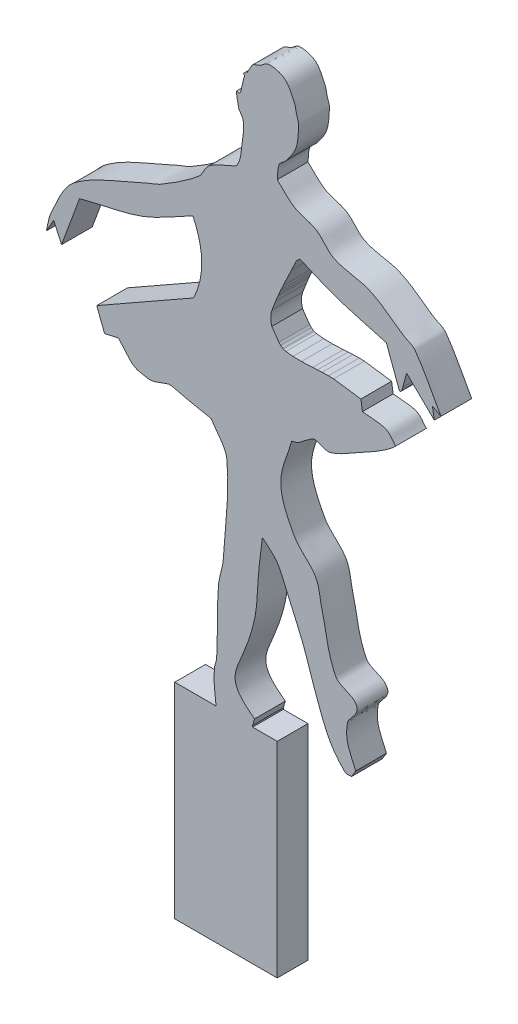
SolidWorks part; units mm, degrees
ref_plane "Alzado" through (0, 0, 0) normal (0, 0, 1) x (1, 0, 0)
ref_plane "Planta" through (0, 0, 0) normal (0, 1, 0) x (1, 0, 0)
ref_plane "Vista lateral" through (0, 0, 0) normal (1, 0, 0) x (0, 0, -1)
sketch "Croquis4" plane through (0, 0, 0) normal (0, 0, 1) x (1, 0, 0)
  line L0 (1069.8862, -9982.1073) -> (1096.5761, -9982.1073) construction
  line L1 (1102.5614, -9982.0997) -> (1101.7304, -9981.6452)
  line L3 (1101.7304, -9981.6452) -> (1101.914, -9982.7471)
  line L4 (1101.914, -9982.7471) -> (1099.2069, -9980.1163)
  line L5 (1099.2069, -9980.1163) -> (1098.8413, -9981.4945)
  line L7 (1098.4831, -9981.9057) -> (1097.2342, -9978.547)
  line L8 (1094.7459, -9984.5391) -> (1094.8984, -9985.5305)
  line L9 (1094.2502, -10016.2238) -> (1093.8308, -10016.9101)
  line L10 (1084.375, -10016.7576) -> (1084.1843, -10017.4058)
  line L12 (1071.1055, -9991.2124) -> (1069.7328, -9991.5175)
  line L13 (1069.7328, -9991.5175) -> (1068.9703, -9989.5348)
  line L14 (1068.9703, -9989.5348) -> (1078.4261, -9984.1587)
  line L15 (1067.2926, -9981.3372) -> (1065.5387, -9986.1032)
  line L16 (1065.5387, -9986.1032) -> (1064.7761, -9984.4256)
  line L17 (1064.7761, -9984.4256) -> (1064.0517, -9985.6838)
  line L19 (1083.4028, -9962.9472) -> (1083.3065, -9962.7305)
  line L20 (1083.3065, -9962.7305) -> (1083.5734, -9962.4636)
  line L21 (1083.5734, -9962.4636) -> (1083.6497, -9962.5018)
  line L27 (1084.1843, -10017.4058) -> (1084.375, -10016.7576)
  line L28 (1057.3314, -9960.8458) -> (1057.3314, -10026.2108)
  line L29 (1080.5994, -10017.3685) -> (1080.6272, -10017.5493)
  line L30 (1076.5856, -10017.5493) -> (1080.6272, -10017.5493)
  line L35 (1076.5856, -10017.5493) -> (1076.5856, -10037.5493)
  line L36 (1076.5856, -10037.5493) -> (1086.5856, -10037.5493)
  line L37 (1086.5856, -10017.5493) -> (1086.5856, -10037.5493)
  line L38 (1084.1843, -10017.4058) -> (1084.1843, -10017.5493)
  line L39 (1084.1843, -10017.5493) -> (1086.5856, -10017.5493)
  line L40 (1094.7459, -9984.5391) -> (1092.0915, -9984.1685)
  line L41 (1092.0915, -9984.1685) -> (1091.5875, -9984.1566)
  line L42 (1091.5875, -9984.1566) -> (1090.9595, -9984.173)
  line L43 (1090.9595, -9984.173) -> (1090.5104, -9984.1966)
  line L44 (1090.5104, -9984.1966) -> (1090.0409, -9984.2251)
  line L45 (1090.0409, -9984.2251) -> (1088.9419, -9984.2732)
  line L46 (1088.9419, -9984.2732) -> (1088.1172, -9984.2538)
  line L47 (1088.1172, -9984.2538) -> (1087.4347, -9984.1733)
  line L48 (1087.4347, -9984.1733) -> (1087.1951, -9984.1113)
  line L49 (1087.1951, -9984.1113) -> (1087.1127, -9984.071)
  line L50 (1087.1127, -9984.071) -> (1086.9204, -9983.9308)
  line L51 (1086.9204, -9983.9308) -> (1086.7524, -9983.7528)
  line L52 (1086.7524, -9983.7528) -> (1086.0567, -9982.7471)
  line L53 (1086.0805, -9981.3372) -> (1086.431, -9980.4183)
  line L54 (1086.431, -9980.4183) -> (1086.6588, -9979.8715)
  line L55 (1086.6588, -9979.8715) -> (1086.785, -9979.5803)
  line L56 (1086.785, -9979.5803) -> (1086.946, -9979.2181)
  line L57 (1086.946, -9979.2181) -> (1087.1661, -9978.7366)
  line L58 (1087.1661, -9978.7366) -> (1087.9738, -9977.0327)
  line L59 (1087.9738, -9977.0327) -> (1088.4623, -9975.9968)
  line L61 (1092.8353, -9977.2977) -> (1094.6199, -9977.8259)
  line L62 (1094.6199, -9977.8259) -> (1095.769, -9978.1393)
  line L63 (1095.769, -9978.1393) -> (1097.2342, -9978.547)
  line L64 (1088.4623, -9975.9968) -> (1088.8004, -9975.6775)
  spline S0 degree 3 poles (1083.6497, -9962.5018) (1083.7591, -9962.2555) (1083.9978, -9961.7956) (1084.1835, -9961.5867) (1084.2975, -9961.4584) (1084.7754, -9961.341) (1084.9461, -9961.2435) (1085.228, -9961.0824) (1085.4602, -9960.7531) (1085.7849, -9960.7478) (1086.3156, -9960.7393) (1086.8987, -9960.87) (1087.31, -9961.2054) (1087.783, -9961.5911) (1087.9974, -9962.2193) (1088.2632, -9962.7687) (1088.3827, -9963.0156) (1088.3887, -9963.3028) (1088.4539, -9963.5693) (1088.5285, -9963.8748) (1088.6976, -9964.1704) (1088.6826, -9964.4844) (1088.5936, -9966.3536) (1088.4856, -9966.726) (1087.4625, -9968.0304) (1087.2629, -9968.2849) (1086.903, -9968.419) (1086.7762, -9968.7167) (1086.5952, -9969.1417) (1086.6491, -9969.6318) (1086.5856, -9970.0893) knots 0 0 0 0 1 1 1 2 2 2 3 3 3 4 4 4 5 5 5 6 6 6 7 7 7 8 8 8 9 9 9 10 10 10 10
  spline S1 degree 3 poles (1086.5856, -9970.0893) (1087.1448, -9970.585) (1087.627, -9971.1843) (1088.2632, -9971.5763) (1088.9042, -9971.9712) (1089.7198, -9972.0195) (1090.3603, -9972.4151) (1091.0347, -9972.8317) (1091.4383, -9973.6342) (1092.1523, -9973.9784) (1093.2469, -9974.506) (1094.5565, -9974.4613) (1095.6601, -9974.9697) (1096.8448, -9975.5155) (1097.8423, -9976.3991) (1098.9392, -9977.1049) (1099.304, -9977.3397) (1099.7902, -9977.4401) (1100.0449, -9977.7912) (1101.0213, -9979.1377) (1101.7226, -9980.6636) (1102.5614, -9982.0997) knots 0 0 0 0 1 1 1 2 2 2 3 3 3 4 4 4 5 5 5 6 6 6 7 7 7 7
  spline S2 degree 3 poles (1097.2342, -9978.547) (1095.5693, -9978.0641) (1093.8765, -9977.6684) (1092.2394, -9977.0981) (1091.0681, -9976.6901) (1089.9383, -9976.1731) (1088.8004, -9975.6775) knots 0 0 0 0 1 1 1 1.797437 1.797437 1.797437 1.797437
  spline S3 degree 3 poles (1098.4831, -9981.9057) (1098.5937, -9982.0964) (1098.7131, -9981.9593) (1098.8413, -9981.4945) knots 0.232918 0.232918 0.232918 0.232918 1 1 1 1
  spline S4 degree 3 poles (1094.8984, -9985.5305) (1095.661, -9985.6449) (1096.4702, -9985.5873) (1097.1861, -9985.8736) (1097.6033, -9986.0405) (1097.8216, -9986.5091) (1098.1393, -9986.8269) knots 0 0 0 0 1 1 1 2 2 2 2
  spline S5 degree 3 poles (1098.1393, -9986.8269) (1097.4278, -9987.5977) (1095.4058, -9988.7216) (1094.4409, -9989.2289) (1093.5403, -9989.7024) (1092.6853, -9990.327) (1091.6956, -9990.5634) (1091.1327, -9990.6979) (1090.4615, -9989.9755) (1089.9799, -9990.2965) (1088.1959, -9991.4858) (1089.1582, -9991.1468) (1087.9972, -9991.4785) knots 0 0 0 0 1 1 1 2 2 2 3 3 3 4 4 4 4
  spline S6 degree 3 poles (1087.9972, -9991.4785) (1087.6413, -9992.8511) (1086.8883, -9994.179) (1086.9296, -9995.5964) (1086.968, -9996.9142) (1087.5912, -9998.1775) (1088.226, -9999.333) (1088.7424, -10000.2729) (1089.7965, -10000.8388) (1090.323, -10001.7732) (1090.7225, -10002.4822) (1090.7262, -10003.3501) (1090.9331, -10004.1371) (1091.3743, -10005.8157) (1091.4763, -10007.6253) (1092.2676, -10009.1701) (1092.6066, -10009.8321) (1093.6246, -10009.85) (1094.1359, -10010.3902) (1094.9321, -10011.2315) (1093.5656, -10011.9451) (1093.4495, -10012.5254) (1093.1321, -10014.1127) (1093.6779, -10014.9109) (1094.2502, -10016.2238) knots 0 0 0 0 1 1 1 2 2 2 3 3 3 4 4 4 5 5 5 6 6 6 7 7 7 8 8 8 8
  spline S7 degree 3 poles (1093.8308, -10016.9101) (1093.6148, -10016.8847) (1093.3378, -10016.9864) (1093.1826, -10016.8339) (1091.7267, -10015.4026) (1091.2933, -10014.1866) (1090.5899, -10012.3347) (1089.889, -10010.4893) (1089.3884, -10008.564) (1088.5691, -10006.768) (1086.4028, -10002.0187) (1087.0812, -10002.6934) (1085.1376, -10001.0487) knots 0 0 0 0 1 1 1 2 2 2 3 3 3 4 4 4 4
  spline S8 degree 3 poles (1085.1376, -10001.0487) (1085.0232, -10001.9892) (1084.8931, -10002.928) (1084.7944, -10003.8702) (1084.6389, -10005.3557) (1084.6934, -10006.872) (1084.375, -10008.3313) (1083.2252, -10013.6011) (1080.7341, -10014.0607) (1084.375, -10016.7576) knots 0 0 0 0 1 1 1 2 2 2 3 3 3 3
  spline S9 degree 3 poles (1080.5994, -10017.3685) (1080.4585, -10016.3352) (1080.3425, -10015.2751) (1080.485, -10014.242) (1080.5208, -10013.9824) (1080.6625, -10013.7411) (1080.6757, -10013.4794) (1080.7772, -10011.4605) (1080.7123, -10009.4351) (1080.8282, -10007.417) (1080.8801, -10006.5136) (1081.2722, -10005.6514) (1081.3239, -10004.748) (1081.4871, -10001.8907) (1081.9661, -9999.0154) (1081.667, -9996.1691) (1081.5599, -9995.1501) (1080.6503, -9994.3898) (1080.1419, -9993.5001) knots 0 0 0 0 1 1 1 2 2 2 3 3 3 4 4 4 5 5 5 6 6 6 6
  spline S10 degree 3 poles (1080.1419, -9993.5001) (1079.1918, -9993.3325) (1078.2617, -9993.1328) (1077.3204, -9992.9282) (1076.8893, -9992.8345) (1076.4649, -9992.6447) (1076.024, -9992.6613) (1075.7269, -9992.6725) (1074.6048, -9993.3114) (1073.9651, -9993.1951) (1073.4979, -9993.1102) (1072.9827, -9993.0844) (1072.5925, -9992.8138) (1071.9938, -9992.3988) (1071.6011, -9991.7462) (1071.1055, -9991.2124) knots 0 0 0 0 1 1 1 2 2 2 3 3 3 4 4 4 5 5 5 5
  spline S11 degree 2 poles (1078.4261, -9984.1587) (1080.0512, -9980.7931) (1078.3499, -9977.2574) knots 0 0 0 0.498057 0.498057 0.498057
  spline S12 degree 3 poles (1078.3499, -9977.2574) (1076.7358, -9978.0836) (1075.2008, -9979.0872) (1073.5075, -9979.7358) (1071.5098, -9980.5011) (1069.3496, -9980.7495) (1067.2926, -9981.3372) knots 0 0 0 0 1 1 1 2 2 2 2
  spline S13 degree 3 poles (1064.0517, -9985.6838) (1064.2207, -9985.0586) (1064.2692, -9984.3874) (1064.5587, -9983.8081) (1065.1797, -9982.5655) (1065.6593, -9981.1184) (1066.7579, -9980.2685) (1068.7451, -9978.731) (1071.238, -9977.992) (1073.4972, -9976.8927) (1074.0915, -9976.6035) (1074.7495, -9976.444) (1075.3163, -9976.1041) (1076.5587, -9975.3589) (1077.7919, -9974.5793) (1078.9037, -9973.6504) (1079.3427, -9973.2837) (1079.4744, -9972.6297) (1079.9135, -9972.2632) (1080.4284, -9971.8334) (1081.1034, -9971.6438) (1081.6923, -9971.3226) (1082.0369, -9971.1346) (1082.5236, -9971.0796) (1082.7134, -9970.736) (1083.0608, -9970.1073) (1083.08, -9969.3435) (1083.1791, -9968.6321) (1083.2651, -9968.0141) (1083.3509, -9967.3806) (1083.2667, -9966.7623) (1083.2192, -9966.4131) (1082.8625, -9966.1618) (1082.7956, -9965.8158) (1082.36, -9963.5631) (1082.7687, -9965.2233) (1083.0418, -9964.3632) (1083.1892, -9963.899) (1083.1912, -9963.3859) (1083.4028, -9962.9472) knots 0 0 0 0 1 1 1 2 2 2 3 3 3 4 4 4 5 5 5 6 6 6 7 7 7 8 8 8 9 9 9 10 10 10 11 11 11 12 12 12 13 13 13 13
  spline S14 degree 2 poles (1086.0567, -9982.7471) (1085.8341, -9982.0014) (1086.0805, -9981.3372) knots 0 0 0 1 1 1
  dimension "D1" = 20
  dimension "D2" = 10
  dimension "D3" = 65.365
extrude "Saliente-Extruir3" add sketch "Croquis4" along normal blind 3 contours L0 S11 L14 L13 L12 S10 S9 L29 L30 L35 L36 L37 L39 L38 L10 S8 S7 L9 S6 S5 S4 L8 L40 L41 L42 L43 L44 L45 L46 L47 L48 L49 L50 L51 L52 S14 | S11 L0 S14 L53 L54 L55 L56 L57 L58 L59 L64 S2 L61 L62 L7 S3 L5 L4 L3 L1 S1 S0 L21 L20 L19 S13 L17 L16 L15 S12
